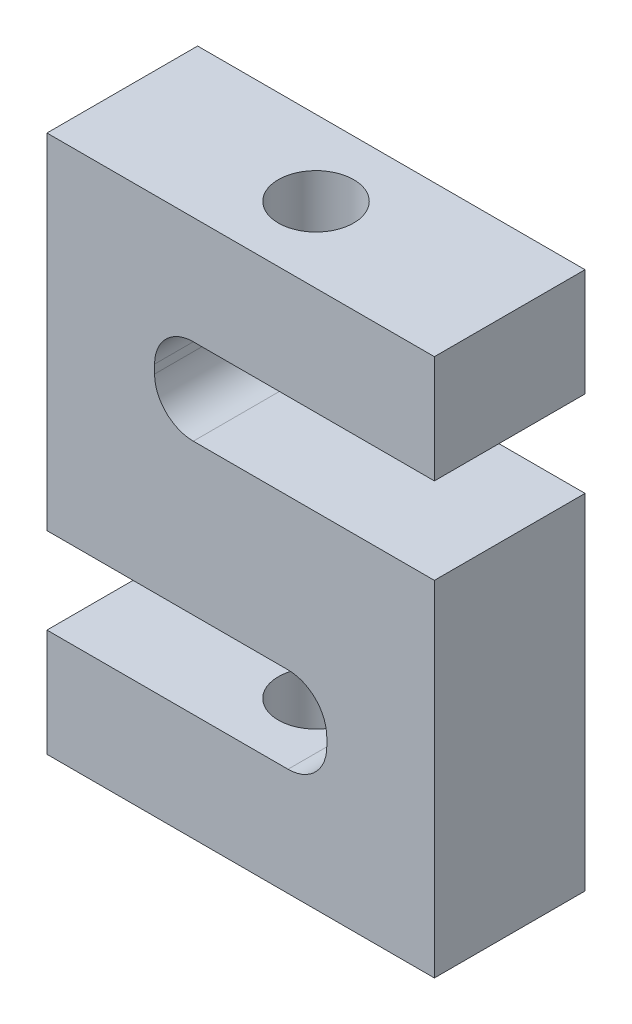
SolidWorks part; units mm, degrees
material "Alloy Steel"
ref_plane "Front Plane" through (0, 0, 0) normal (0, 0, 1) x (1, 0, 0)
ref_plane "Top Plane" through (0, 0, 0) normal (0, 1, 0) x (1, 0, 0)
ref_plane "Right Plane" through (0, 0, 0) normal (1, 0, 0) x (0, 0, -1)
sketch "Sketch1" plane through (0, 0, 0) normal (0, 0, 1) x (1, 0, 0)
  line L0 (82.55, 0) -> (0, 0)
  line L1 (82.55, 0) -> (82.55, -101.6)
  line L2 (82.55, -101.6) -> (-31.75, -101.6)
  line L3 (-31.75, -101.6) -> (-31.75, -69.85)
  line L4 (-31.75, -69.85) -> (50.8, -69.85)
  line L5 (50.8, -69.85) -> (50.8, -44.45)
  line L6 (50.8, -44.45) -> (-31.75, -44.45)
  line L7 (-31.75, -44.45) -> (-31.75, 57.15)
  line L8 (-31.75, 57.15) -> (82.55, 57.15)
  line L9 (82.55, 57.15) -> (82.55, 25.4)
  line L10 (82.55, 25.4) -> (0, 25.4)
  line L11 (0, 25.4) -> (0, 0)
  dimension "D1" = 101.6
  dimension "D2" = 31.75
  dimension "D3" = 25.4
  dimension "D4" = 31.75
  dimension "D5" = 114.3
extrude "Boss-Extrude1" add sketch "Sketch1" along normal blind 44.45
fillet "Fillet1" radius 11.43 4 edges at (50.8, -69.85, 22.225) (50.8, -44.45, 22.225) (0, 25.4, 22.225) (0, 0, 22.225)
sketch "Sketch2" plane through (0, 57.15, 0) normal (0, 1, 0) x (1, 0, 0)
  line L0 (25.4, 0) -> (25.4, -44.45) construction
  line L1 (82.55, 0) -> (-31.75, 0) construction
  line L2 (82.55, -44.45) -> (-31.75, -44.45) construction
  point P6 (25.4, -22.225)
sketch "Sketch3" plane through (0, -101.6, 0) normal (0, -1, 0) x (1, 0, 0)
  line L0 (25.4, 44.45) -> (25.4, 0) construction
  line L1 (-31.75, 44.45) -> (82.55, 44.45) construction
  line L2 (-31.75, 0) -> (82.55, 0) construction
  point P6 (25.4, 22.225)
hole_wizard "1-8 Tapped Hole1" positions "Sketch5" profile "Sketch4" tap size "1-8" standard "Ansi Inch" end condition up to next
sketch "Sketch5" plane through (0, -101.6, 0) normal (0, -1, 0) x (1, 0, 0)
  point P1 (25.4, 22.225)
cosmetic thread "Hole Thread1" parameters "D2"=25.4
sketch "Sketch4" plane through (25.4, -101.6, 22.225) normal (1, 0, 0) x (0, 0, -1)
  line L0 (0, 0) -> (0, 31.75)
  line L1 (0, 31.75) -> (11.1125, 31.75)
  line L2 (11.1125, 31.75) -> (11.1125, 0)
  line L5 (11.1125, 0) -> (0, 0)
  line L11 (0, -6.35) -> (0, 107.95) construction
  dimension "Thru Tap Drill Dia." = 22.225
  dimension "Thru Tap Drill Depth" = 31.75
hole_wizard "1-8 Tapped Hole2" positions "Sketch7" profile "Sketch6" tap size "1-8" standard "Ansi Inch" end condition up to next
sketch "Sketch7" plane through (0, 57.15, 0) normal (0, 1, 0) x (-1, 0, 0)
  point P1 (-25.4, 22.225)
cosmetic thread "Hole Thread2" parameters "D2"=25.4
sketch "Sketch6" plane through (25.4, 57.15, 22.225) normal (1, 0, 0) x (0, 0, 1)
  line L0 (0, 0) -> (0, 31.75)
  line L1 (0, 31.75) -> (11.1125, 31.75)
  line L2 (11.1125, 31.75) -> (11.1125, 0)
  line L5 (11.1125, 0) -> (0, 0)
  line L11 (0, -6.35) -> (0, 107.95) construction
  dimension "Thru Tap Drill Dia." = 22.225
  dimension "Thru Tap Drill Depth" = 31.75
